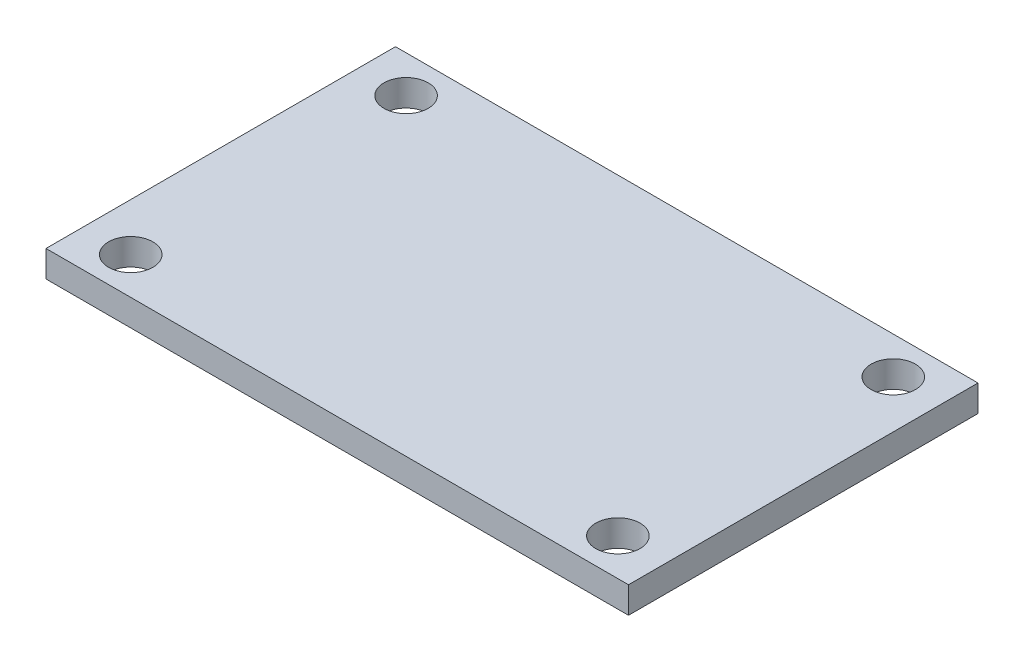
SolidWorks part; units mm, degrees
ref_plane "Front Plane" through (0, 0, 0) normal (0, 0, 1) x (1, 0, 0)
ref_plane "Top Plane" through (0, 0, 0) normal (0, 1, 0) x (1, 0, 0)
ref_plane "Right Plane" through (0, 0, 0) normal (1, 0, 0) x (0, 0, -1)
sketch "Sketch1" plane through (0, 0, 0) normal (0, 1, 0) x (1, 0, 0)
  line L1 (-42.7686, 22.2552) -> (27.0814, 22.2552)
  line L2 (-42.7686, 22.2552) -> (-42.7686, -19.6548)
  line L3 (-42.7686, -19.6548) -> (27.0814, -19.6548)
  line L4 (27.0814, 22.2552) -> (27.0814, -19.6548)
  dimension "D1" = 69.85
  dimension "D2" = 41.91
extrude "Boss-Extrude1" add sketch "Sketch1" along normal blind 3.175
hole_wizard "F size bit 1/4 Clearance Hole1" positions "Sketch12" profile "Sketch11" hole size "#4" standard "Ansi Inch"
sketch "Sketch12" plane through (0, 3.175, 0) normal (0, 1, 0) x (-1, 0, 0)
  line L2 (42.7686, 19.6548) -> (-27.0814, 19.6548) construction
  line L3 (42.7686, -22.2552) -> (42.7686, 19.6548) construction
  point P6 (37.0536, 15.2098)
  point P9 (-21.3664, 15.2098)
  point P11 (-21.3664, -17.8102)
  point P13 (37.0536, -17.8102)
  dimension "D3" = 58.42
  dimension "D4" = 58.42
  dimension "D5" = 33.02
  dimension "D6" = 33.02
  dimension "D7" = 4.445
  dimension "D8" = 5.715
sketch "Sketch11" plane through (-37.0536, 3.175, 15.2098) normal (1, 0, 0) x (0, 0, 1)
  line L0 (0, 0) -> (0, 14.2949)
  line L1 (0, 14.2949) -> (2.6543, 12.7)
  line L2 (2.6543, 12.7) -> (2.6543, 0)
  line L5 (2.6543, 0) -> (0, 0)
  line L10 (0, 14.2949) -> (-2.6543, 12.7) construction
  line L11 (0, -6.35) -> (0, 107.95) construction
  dimension "Hole Dia." = 5.3086
  dimension "Hole Depth" = 12.7
  dimension "Drill Angle" = 118
hole_wizard "Tap Drill for M3x0.5 Tap1" positions "Sketch15" profile "Sketch14" hole size "M3x0.5" standard "Ansi Metric"
sketch "Sketch15" plane through (0, 0, 0) normal (0, -1, 0) x (1, 0, 0)
  line L0 (-42.7686, -22.2552) -> (-42.7686, 19.6548) construction
  line L1 (-42.7686, 19.6548) -> (27.0814, 19.6548) construction
  point P0 (-29.4336, 15.8448)
  dimension "D1" = 13.335
  dimension "D2" = 3.81
sketch "Sketch14" plane through (-29.4336, 0, 15.8448) normal (1, 0, 0) x (0, 0, -1)
  line L0 (0, 0) -> (0, 3.0371)
  line L1 (0, 3.0371) -> (1.25, 2.286)
  line L2 (1.25, 2.286) -> (1.25, 0)
  line L5 (1.25, 0) -> (0, 0)
  line L10 (0, 3.0371) -> (-1.25, 2.286) construction
  line L11 (0, -6.35) -> (0, 107.95) construction
  dimension "Hole Dia." = 2.5
  dimension "Hole Depth" = 2.286
  dimension "Drill Angle" = 118
pattern_linear "LPattern2" count 2 spacing 43.18 along (1, 0, 0) count 2 spacing 34.29 along (0, 0, -1) of "Tap Drill for M3x0.5 Tap1"
equation "\"D1@Sketch15\" = (\"D1@Sketch1\"-\"RD3@Annotations\")/2"
equation "\"D7@Sketch12\" = (\"RD1@Annotations\"-\"D6@Sketch12\")/2"
equation "\"D8@Sketch12\" = (\"RD4@Annotations\"-\"D3@Sketch12\")/2"
